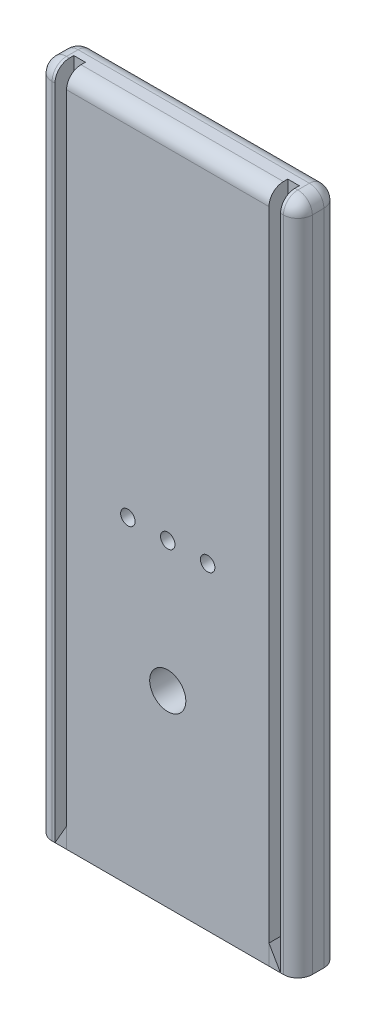
SolidWorks part; units mm, degrees
material "Oak"
ref_plane "Front Plane" through (0, 0, 0) normal (0, 0, 1) x (1, 0, 0)
ref_plane "Top Plane" through (0, 0, 0) normal (0, 1, 0) x (1, 0, 0)
ref_plane "Right Plane" through (0, 0, 0) normal (1, 0, 0) x (0, 0, -1)
sketch "Sketch1" plane through (0, 0, 0) normal (0, 0, 1) x (1, 0, 0)
  line L1 (-57.15, -147.6375) -> (57.15, -147.6375)
  line L2 (-57.15, -147.6375) -> (-57.15, 147.6375)
  line L3 (-57.15, 147.6375) -> (57.15, 147.6375)
  line L4 (57.15, -147.6375) -> (57.15, 147.6375)
  line L5 (-57.15, -147.6375) -> (57.15, 147.6375) construction
  line L6 (-57.15, 147.6375) -> (57.15, -147.6375) construction
  point P0 (0, 0)
  dimension "D1" = 114.3
  dimension "D2" = 295.275
extrude "Boss-Extrude1" add sketch "Sketch1" along normal mid plane 17.78
sketch "Sketch2" plane through (0, 0, 8.89) normal (0, 0, 1) x (1, 0, 0)
  line L1 (-57.15, -147.6375) -> (57.15, -147.6375) construction
  circle A0 centre (0, -7.9375) radius 3.175
  circle A1 centre (-17.526, -7.9375) radius 3.175
  circle A2 centre (17.526, -7.9375) radius 3.175
  dimension "D1" = 6.35
  dimension "D2" = 139.7
  dimension "D3" = 17.526
  dimension "D4" = 17.526
extrude "Cut-Extrude1" cut sketch "Sketch2" against normal blind 12.7
sketch "Sketch3" plane through (0, 147.6375, 0) normal (0, 1, 0) x (1, 0, 0)
  line L0 (57.15, -8.89) -> (-57.15, -8.89) construction
  line L1 (-49.53, -8.89) -> (-44.45, -8.89)
  line L2 (-49.53, -8.89) -> (-49.53, -0.635)
  line L3 (-49.53, -0.635) -> (-44.45, -0.635)
  line L4 (-44.45, -8.89) -> (-44.45, -0.635)
  dimension "D1" = 5.08
  dimension "D2" = 8.255
  dimension "D3" = 44.45
extrude "Cut-Extrude2" cut sketch "Sketch3" against normal through all
mirror "Mirror1" about plane through (0, 0, 0) normal (1, 0, 0) of "Cut-Extrude2"
sketch "Sketch4" plane through (0, 0, -8.89) normal (0, 0, -1) x (-1, 0, 0)
  line L0 (57.15, -147.6375) -> (-57.15, -147.6375) construction
  line L1 (-31.75, -52.3875) -> (31.75, -52.3875)
  line L2 (-31.75, -52.3875) -> (-31.75, -71.4375)
  line L3 (-31.75, -71.4375) -> (31.75, -71.4375)
  line L4 (31.75, -52.3875) -> (31.75, -71.4375)
  line L5 (-31.75, -52.3875) -> (31.75, -71.4375) construction
  line L6 (-31.75, -71.4375) -> (31.75, -52.3875) construction
  line L7 (-57.15, -147.6375) -> (-57.15, 147.6375) construction
  line L8 (57.15, 147.6375) -> (57.15, -147.6375) construction
  point P0 (0, -61.9125)
  dimension "D1" = 76.2
  dimension "D2" = 19.05
  dimension "D3" = 25.4
  dimension "D4" = 25.4
extrude "Cut-Extrude3" [suppressed] cut sketch "Sketch4" against normal through all
fillet "Fillet1" radius 6.35 10 edges at (57.15, 0, -8.89) (0, 147.6375, -8.89) (57.15, 0, 8.89) (-53.34, 147.6375, 8.89) (0, 147.6375, 8.89) (53.34, 147.6375, 8.89) (-57.15, 147.6375, 0) (57.15, 147.6375, 0) (-57.15, 0, -8.89) (-57.15, 0, 8.89)
sketch "Sketch5" plane through (0, 0, 8.89) normal (0, 0, 1) x (1, 0, 0)
  line L0 (-44.45, -147.6375) -> (44.45, -147.6375) construction
  line L1 (57.15, 141.2875) -> (57.15, -147.6375) construction
  circle A0 centre (0, -65.0875) radius 7.9375
  dimension "D1" = 15.875
  dimension "D2" = 82.55
  dimension "D3" = 57.15
extrude "Cut-Extrude4" cut sketch "Sketch5" against normal through all
chamfer "Chamfer1" [suppressed] distance 12.7 distance2 19.05
chamfer "Chamfer2" [suppressed] distance 19.05 angle 30
sketch "Sketch6" plane through (0, 0, 0.635) normal (0, 0, 1) x (1, 0, 0)
  line L0 (-49.53, -147.6375) -> (-44.45, -138.8408)
  line L1 (-44.45, -147.6375) -> (-44.45, 147.6375) construction
  line L2 (-44.45, -138.8408) -> (-44.45, -147.6375)
  line L3 (-44.45, -147.6375) -> (-49.53, -147.6375)
  line L4 (49.53, -147.6375) -> (44.45, -138.8408)
  line L5 (44.45, -147.6375) -> (44.45, 147.6375) construction
  line L6 (44.45, -138.8408) -> (44.45, -147.6375)
  line L7 (44.45, -147.6375) -> (49.53, -147.6375)
extrude "Boss-Extrude5" add sketch "Sketch6" along direction (0, 0, -1) on the side of the normal up to vertex (8.255 mm away) separate body
equation "\".70.10in\"=0.1"
